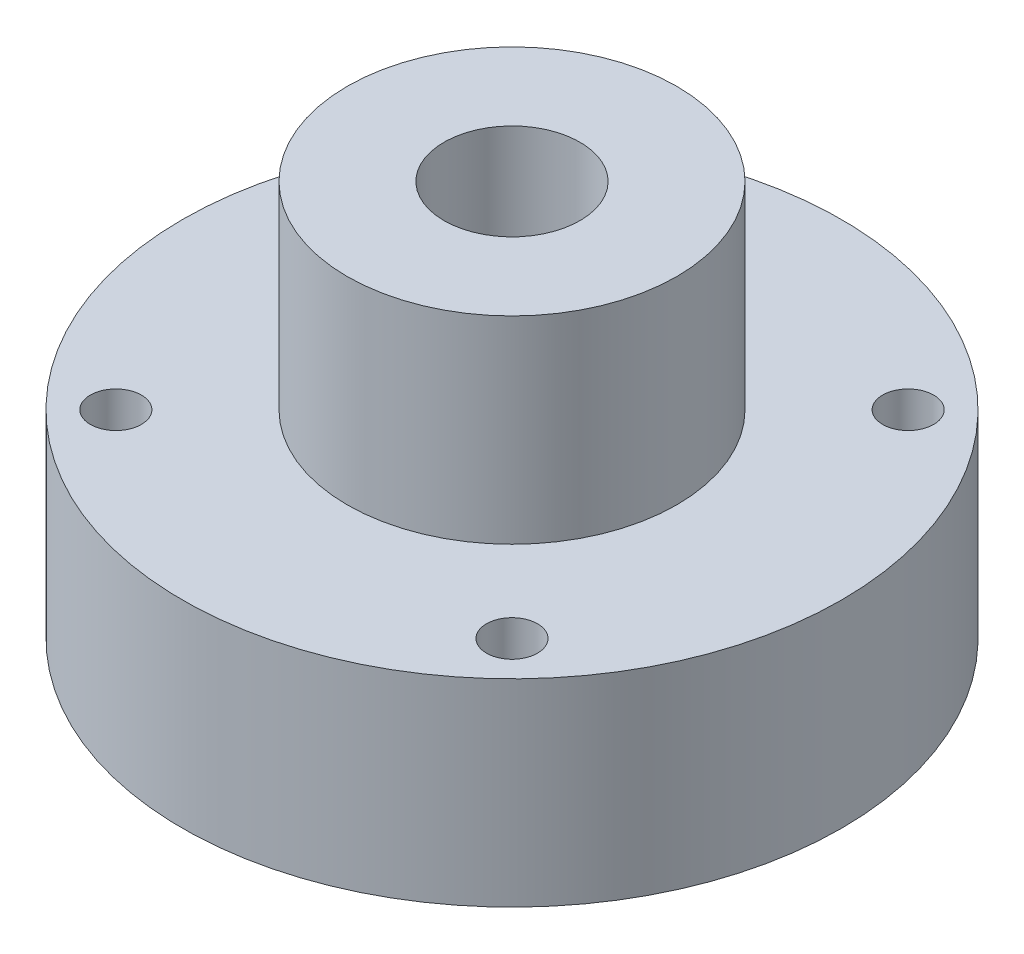
SolidWorks part; units mm, degrees
material "6061-T6 (SS)"
ref_plane "Front Plane" through (0, 0, 0) normal (0, 0, 1) x (1, 0, 0)
ref_plane "Top Plane" through (0, 0, 0) normal (0, 1, 0) x (1, 0, 0)
ref_plane "Right Plane" through (0, 0, 0) normal (1, 0, 0) x (0, 0, -1)
sketch "Sketch1" plane through (0, 0, 0) normal (0, 0, 1) x (1, 0, 0)
  line L0 (0, 0) -> (0, -5.2937) construction
  line L6 (-12.7, -19.05) -> (-12.7, -38.1)
  line L9 (-31.75, 0) -> (-31.75, -38.1)
  line L12 (-12.7, -19.05) -> (-3.175, -19.05)
  line L15 (-19.0373, -38.1) -> (-12.7, -38.1)
  line L17 (-31.75, -38.1) -> (-23.8125, -38.1)
  line L18 (-23.8125, -38.1) -> (-23.8125, -34.9631)
  line L19 (-23.8125, -34.9631) -> (-19.0373, -34.9631)
  line L20 (-19.0373, -34.9631) -> (-19.0373, -38.1)
  line L24 (-12.7, -38.1) -> (-3.175, -19.05)
  line L25 (-31.75, 0) -> (-3.175, 0)
  line L26 (-3.175, 0) -> (-3.175, -19.05)
  line L27 (-31.75, -19.05) -> (-15.875, -19.05)
  line L28 (-15.875, -19.05) -> (-15.875, 0)
  spline S0 degree 3 poles (6.8653, -14.0383) (6.7746, -14.0297) (6.669, -14.0211) (6.2404, -13.9904) (5.8365, -13.9684) (4.8724, -13.9243) (4.3124, -13.9022) (3.084, -13.8581) (2.4159, -13.8361) (1.0289, -13.792) (0.3103, -13.77) (-1.1159, -13.7259) (-1.8233, -13.7038) (-3.1659, -13.6597) (-3.8009, -13.6377) (-4.9442, -13.5936) (-5.4523, -13.5715) (-6.2976, -13.5274) (-6.6348, -13.5054) (-7.1093, -13.4613) (-7.3837, -13.4172) (-7.2343, -13.3731) (-6.8792, -13.329) (-6.5989, -13.3069) (-5.8566, -13.2628) (-5.3947, -13.2408) (-4.3289, -13.1967) (-3.7251, -13.1746) (-2.4274, -13.1305) (-1.7337, -13.1085) (-0.3158, -13.0644) (0.4082, -13.0423) (1.8242, -12.9983) (2.5161, -12.9762) (3.8083, -12.9321) (4.4084, -12.9101) (5.4653, -12.866) (5.922, -12.8439) (6.6525, -12.7998) (6.9263, -12.7778) (7.2673, -12.7337) (7.4017, -12.6896) (7.1111, -12.6455) (6.6204, -12.6014) (6.275, -12.5793) (5.4137, -12.5352) (4.8979, -12.5132) (3.74, -12.4691) (3.0981, -12.447) (1.7433, -12.4029) (1.0305, -12.3809) (-0.4048, -12.3368) (-1.1271, -12.3147) (-2.5192, -12.2706) (-3.1888, -12.2486) (-4.4177, -12.2045) (-4.9769, -12.1825) (-5.9368, -12.1384) (-6.3373, -12.1163) (-6.9452, -12.0722) (-7.1525, -12.0502) (-7.3559, -12.0061) (-7.352, -11.984) (-7.1332, -11.9399) (-6.9183, -11.9179) (-6.2959, -11.8738) (-5.8884, -11.8517) (-4.9158, -11.8076) (-4.3507, -11.7856) (-3.1114, -11.7415) (-2.4374, -11.7194) (-1.0381, -11.6753) (-0.313, -11.6533) (1.1259, -11.6092) (1.8395, -11.5871) (3.194, -11.543) (3.8347, -11.521) (4.9881, -11.4769) (5.5007, -11.4548) (6.3536, -11.4108) (6.6938, -11.3887) (7.1724, -11.3446) (7.4493, -11.3005) (7.2985, -11.2564) (6.9403, -11.2123) (6.6574, -11.1903) (5.9085, -11.1462) (5.4425, -11.1241) (4.3673, -11.08) (3.7581, -11.058) (2.4489, -11.0139) (1.749, -10.9918) (0.3186, -10.9477) (-0.4118, -10.9257) (-1.8404, -10.8816) (-2.5384, -10.8595) (-3.842, -10.8154) (-4.4475, -10.7934) (-5.5138, -10.7493) (-5.9745, -10.7272) (-6.7114, -10.6831) (-6.9876, -10.6611) (-7.3316, -10.617) (-7.4672, -10.5729) (-7.174, -10.5288) (-6.679, -10.4847) (-6.3305, -10.4627) (-5.4616, -10.4186) (-4.9412, -10.3965) (-3.7731, -10.3524) (-3.1255, -10.3304) (-1.7587, -10.2863) (-1.0396, -10.2642) (0.4084, -10.2201) (1.1371, -10.1981) (2.5414, -10.154) (3.217, -10.1319) (4.4567, -10.0878) (5.0209, -10.0658) (5.9892, -10.0217) (6.3932, -9.9996) (7.0065, -9.9555) (7.2156, -9.9335) (7.4209, -9.8894) (7.4169, -9.8673) (7.1962, -9.8233) (6.9794, -9.8012) (6.3515, -9.7571) (5.9404, -9.7351) (4.9591, -9.691) (4.3891, -9.6689) (3.1389, -9.6248) (2.4589, -9.6028) (1.0472, -9.5587) (0.3158, -9.5366) (-1.1358, -9.4925) (-1.8557, -9.4705) (-3.2221, -9.4264) (-3.8685, -9.4043) (-5.0321, -9.3602) (-5.5491, -9.3382) (-6.4095, -9.2941) (-6.7527, -9.272) (-7.2356, -9.2279) (-7.5148, -9.1838) (-7.3627, -9.1397) (-7.0013, -9.0956) (-6.716, -9.0736) (-5.9605, -9.0295) (-5.4904, -9.0075) (-4.4056, -8.9634) (-3.7911, -8.9413) (-2.4704, -8.8972) (-1.7644, -8.8752) (-0.3214, -8.8311) (0.4154, -8.809) (1.8566, -8.7649) (2.5607, -8.7429) (3.8757, -8.6988) (4.4865, -8.6767) (5.5622, -8.6326) (6.0269, -8.6106) (6.7704, -8.5665) (7.049, -8.5444) (7.396, -8.5003) (7.5327, -8.4562) (7.237, -8.4121) (6.7375, -8.368) (6.386, -8.346) (5.5095, -8.3019) (4.9846, -8.2798) (3.8062, -8.2358) (3.1529, -8.2137) (1.7741, -8.1696) (1.0487, -8.1476) (-0.412, -8.1035) (-1.147, -8.0814) (-2.5637, -8.0373) (-3.2451, -8.0153) (-4.4958, -7.9712) (-5.0648, -7.9491) (-6.0416, -7.905) (-6.4492, -7.883) (-7.0678, -7.8389) (-7.2788, -7.8168) (-7.4858, -7.7727) (-7.4818, -7.7507) (-7.2591, -7.7066) (-7.0404, -7.6845) (-6.407, -7.6404) (-5.9923, -7.6184) (-5.0025, -7.5743) (-4.4275, -7.5522) (-3.1663, -7.5081) (-2.4803, -7.4861) (-1.0564, -7.442) (-0.3185, -7.42) (1.1457, -7.3759) (1.8719, -7.3538) (3.2503, -7.3097) (3.9023, -7.2877) (5.076, -7.2436) (5.5976, -7.2215) (6.4655, -7.1774) (6.8116, -7.1554) (7.2987, -7.1113) (7.5804, -7.0672) (7.4269, -7.0231) (7.0624, -6.979) (6.7746, -6.9569) (6.0125, -6.9128) (5.5382, -6.8908) (4.444, -6.8467) (3.8242, -6.8246) (2.492, -6.7805) (1.7798, -6.7585) (0.3242, -6.7144) (-0.4191, -6.6923) (-1.8727, -6.6483) (-2.583, -6.6262) (-3.9095, -6.5821) (-4.5256, -6.5601) (-5.6106, -6.516) (-6.0794, -6.4939) (-6.8293, -6.4498) (-7.1103, -6.4278) (-7.4603, -6.3837) (-7.5982, -6.3396) (-7.2999, -6.2955) (-6.7961, -6.2514) (-6.4416, -6.2293) (-5.5574, -6.1852) (-5.0279, -6.1632) (-3.8393, -6.1191) (-3.1803, -6.097) (-1.7895, -6.0529) (-1.0578, -6.0309) (0.4155, -5.9868) (1.157, -5.9647) (2.586, -5.9206) (3.2733, -5.8986) (4.5348, -5.8545) (5.1088, -5.8325) (6.094, -5.7884) (6.5052, -5.7663) (7.1291, -5.7222) (7.3419, -5.7002) (7.5507, -5.6561) (7.5467, -5.634) (7.322, -5.5899) (7.1015, -5.5679) (6.4625, -5.5238) (6.0443, -5.5017) (5.0458, -5.4576) (4.4658, -5.4356) (3.1937, -5.3915) (2.5018, -5.3694) (1.0655, -5.3253) (0.3213, -5.3033) (-1.1556, -5.2592) (-1.8881, -5.2371) (-3.2784, -5.193) (-3.936, -5.171) (-5.1199, -5.1269) (-5.646, -5.1048) (-6.5214, -5.0608) (-6.8705, -5.0387) (-7.3618, -4.9946) (-7.6459, -4.9505) (-7.4912, -4.9064) (-7.1234, -4.8623) (-6.8331, -4.8403) (-6.0644, -4.7962) (-5.5861, -4.7741) (-4.4824, -4.73) (-3.8572, -4.708) (-2.5135, -4.6639) (-1.7951, -4.6418) (-0.327, -4.5977) (0.4227, -4.5757) (1.8889, -4.5316) (2.6053, -4.5095) (3.9432, -4.4654) (4.5646, -4.4434) (5.659, -4.3993) (6.1318, -4.3772) (6.8882, -4.3331) (7.1716, -4.3111) (7.5246, -4.267) (7.6637, -4.2229) (7.3628, -4.1788) (6.8547, -4.1347) (6.4971, -4.1127) (5.6053, -4.0686) (5.0712, -4.0465) (3.8723, -4.0024) (3.2077, -3.9804) (1.8049, -3.9363) (1.0669, -3.9142) (-0.4191, -3.8701) (-1.167, -3.8481) (-2.6082, -3.804) (-3.3015, -3.7819) (-4.5226, -3.7396) (-5.0592, -3.7193) (-5.5281, -3.6991) knots 0.041447 0.041447 0.041447 0.041447 0.042969 0.042969 0.046875 0.046875 0.050781 0.050781 0.054688 0.054688 0.058594 0.058594 0.0625 0.0625 0.066406 0.066406 0.070312 0.070312 0.074219 0.074219 0.078125 0.082031 0.082031 0.085938 0.085938 0.089844 0.089844 0.09375 0.09375 0.097656 0.097656 0.101562 0.101562 0.105469 0.105469 0.109375 0.109375 0.113281 0.113281 0.117188 0.117188 0.121094 0.125 0.125 0.128906 0.128906 0.132812 0.132812 0.136719 0.136719 0.140625 0.140625 0.144531 0.144531 0.148438 0.148438 0.152344 0.152344 0.15625 0.15625 0.160156 0.160156 0.164062 0.164062 0.167969 0.167969 0.171875 0.171875 0.175781 0.175781 0.179688 0.179688 0.183594 0.183594 0.1875 0.1875 0.191406 0.191406 0.195312 0.195312 0.199219 0.199219 0.203125 0.207031 0.207031 0.210938 0.210938 0.214844 0.214844 0.21875 0.21875 0.222656 0.222656 0.226562 0.226562 0.230469 0.230469 0.234375 0.234375 0.238281 0.238281 0.242188 0.242188 0.246094 0.25 0.25 0.253906 0.253906 0.257812 0.257812 0.261719 0.261719 0.265625 0.265625 0.269531 0.269531 0.273438 0.273438 0.277344 0.277344 0.28125 0.28125 0.285156 0.285156 0.289062 0.289062 0.292969 0.292969 0.296875 0.296875 0.300781 0.300781 0.304688 0.304688 0.308594 0.308594 0.3125 0.3125 0.316406 0.316406 0.320312 0.320312 0.324219 0.324219 0.328125 0.332031 0.332031 0.335938 0.335938 0.339844 0.339844 0.34375 0.34375 0.347656 0.347656 0.351562 0.351562 0.355469 0.355469 0.359375 0.359375 0.363281 0.363281 0.367188 0.367188 0.371094 0.375 0.375 0.378906 0.378906 0.382812 0.382812 0.386719 0.386719 0.390625 0.390625 0.394531 0.394531 0.398438 0.398438 0.402344 0.402344 0.40625 0.40625 0.410156 0.410156 0.414062 0.414062 0.417969 0.417969 0.421875 0.421875 0.425781 0.425781 0.429688 0.429688 0.433594 0.433594 0.4375 0.4375 0.441406 0.441406 0.445312 0.445312 0.449219 0.449219 0.453125 0.457031 0.457031 0.460938 0.460938 0.464844 0.464844 0.46875 0.46875 0.472656 0.472656 0.476562 0.476562 0.480469 0.480469 0.484375 0.484375 0.488281 0.488281 0.492188 0.492188 0.496094 0.5 0.5 0.503906 0.503906 0.507812 0.507812 0.511719 0.511719 0.515625 0.515625 0.519531 0.519531 0.523438 0.523438 0.527344 0.527344 0.53125 0.53125 0.535156 0.535156 0.539062 0.539062 0.542969 0.542969 0.546875 0.546875 0.550781 0.550781 0.554688 0.554688 0.558594 0.558594 0.5625 0.5625 0.566406 0.566406 0.570312 0.570312 0.574219 0.574219 0.578125 0.582031 0.582031 0.585938 0.585938 0.589844 0.589844 0.59375 0.59375 0.597656 0.597656 0.601562 0.601562 0.605469 0.605469 0.609375 0.609375 0.613281 0.613281 0.617188 0.617188 0.621094 0.625 0.625 0.628906 0.628906 0.632812 0.632812 0.636719 0.636719 0.640625 0.640625 0.644531 0.644531 0.648438 0.648438 0.652029 0.652029 0.652029 0.652029 construction
  dimension "D2" = 25.4
  dimension "D3" = 19.05
  dimension "D4" = 6.35
  dimension "D5" = 38.1
  dimension "D6" = 26.565
  dimension "D7" = 63.5
  dimension "D8" = 31.75
  dimension "D9" = 4.7752
  dimension "D10" = 19.05
  dimension "D12" = 47.625
  dimension "D13" = 3.1369
revolve "Revolve1" add sketch "Sketch1" angle 360 about L0
hole_wizard "#10 (0.1935) Diameter Hole1" positions "Sketch2" profile "Sketch3" hole size "#10" standard "ANSI Inch" end condition through all
sketch "Sketch2" plane through (0, 0, 0) normal (0, 1, 0) x (1, 0, 0)
  line L0 (-19.083, 19.083) -> (19.083, -19.083) construction
  line L2 (19.083, 19.083) -> (-19.083, -19.083) construction
  line L3 (0, 0) -> (-24.6236, 0) construction
  point P0 (19.083, 19.083)
  point P2 (-19.083, 19.083)
  point P4 (-19.083, -19.083)
  point P6 (19.083, -19.083)
  dimension "D1" = 53.975
  dimension "D2" = 45
sketch "Sketch3" plane through (19.083, 0, -19.083) normal (1, 0, 0) x (0, 0, 1)
  line L0 (0, 0) -> (0, 38.1)
  line L1 (0, 38.1) -> (2.4574, 38.1)
  line L2 (2.4574, 38.1) -> (2.4574, 0)
  line L5 (2.4574, 0) -> (0, 0)
  line L11 (0, -6.35) -> (0, 107.95) construction
  dimension "Thru Hole Dia." = 4.9149
  dimension "Thru Hole Depth" = 38.1
hole_wizard "33/64 (0.51563) Diameter Hole1" positions "3DSketch1" profile "Sketch4" hole size "33/64" standard "ANSI Inch" end condition through all
sketch3d "3DSketch1"
  circle A3 centre (0, 0, 0) radius 3.175 construction
  point P0 (0, 0, 0)
  point P21 (0, 3.175, 0)
  point P24 (0, 0, 0)
sketch "Sketch4" plane through (0, 0, 0) normal (1, 0, 0) x (0, 0, 1)
  line L0 (0, 0) -> (0, 38.1)
  line L1 (0, 38.1) -> (6.5485, 38.1)
  line L2 (6.5485, 38.1) -> (6.5485, 0)
  line L5 (6.5485, 0) -> (0, 0)
  line L11 (0, -6.35) -> (0, 107.95) construction
  dimension "Thru Hole Dia." = 13.097
  dimension "Thru Hole Depth" = 38.1
sketch "Sketch5" plane through (0, -38.1, 0) normal (0, 1, 0) x (1, 0, 0)
  circle A0 centre (0, 0) radius 38.1
  dimension "D1" = 76.2
ref_plane "Plane1" through (0, 0, 0) normal (0, -1, 0) x (-1, 0, 0)
